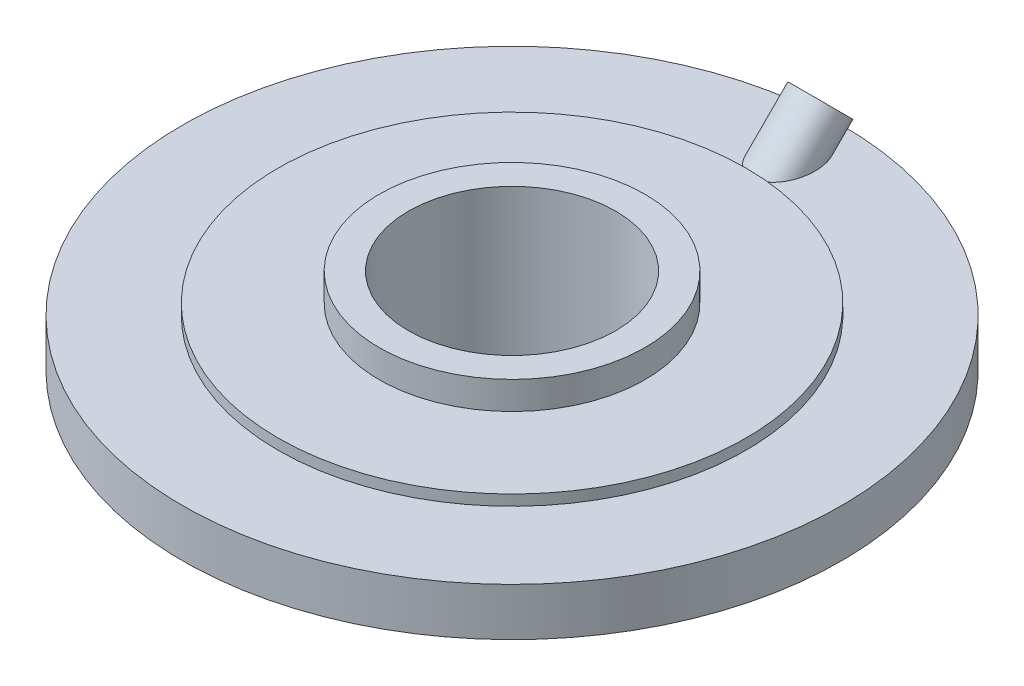
SolidWorks part; units mm, degrees
ref_plane "Front Plane" through (0, 0, 0) normal (0, 0, 1) x (1, 0, 0)
ref_plane "Top Plane" through (0, 0, 0) normal (0, 1, 0) x (1, 0, 0)
ref_plane "Right Plane" through (0, 0, 0) normal (1, 0, 0) x (0, 0, -1)
sketch "Sketch1" plane through (0, 0, 0) normal (0, 0, 1) x (1, 0, 0)
  line L0 (0, 0) -> (25, 0)
  line L1 (25, 0) -> (25, -5.2365)
  line L2 (25, -5.2365) -> (44, -5.2365)
  line L3 (44, -5.2365) -> (44, -7.2365)
  line L4 (44, -7.2365) -> (62, -7.2365)
  line L5 (62, -7.2365) -> (62, -16.2365)
  line L6 (62, -16.2365) -> (30.5, -16.2365)
  line L7 (30.5, -16.2365) -> (30.5, -19.2365)
  line L8 (30.5, -19.2365) -> (26, -19.2365)
  line L9 (26, -19.2365) -> (26, -38.0068)
  line L10 (26, -38.0068) -> (0, -38.0068)
  line L11 (0, -38.0068) -> (0, 0)
  point P3 (0, 0)
  point P14 (0, 0)
  point P15 (0, 0)
  point P16 (0, 0)
  point P17 (0, 0)
  dimension "D1" = 25
  dimension "D2" = 9
  dimension "D3" = 2
  dimension "D4" = 44
  dimension "D5" = 3
  dimension "D6" = 62
  dimension "D7" = 30.5
  dimension "D8" = 26
revolve "Revolve2" add sketch "Sketch1" angle 360 about L11
sketch "Sketch2" plane through (0, 0, 0) normal (0, 1, 0) x (1, 0, 0)
  circle A0 centre (0, 0) radius 19.5
  dimension "D1" = 39
extrude "Cut-Extrude1" cut sketch "Sketch2" against normal blind 90
sketch "Sketch4" plane through (0, 0, 0) normal (1, 0, 0) x (0, 0, -1)
  line L0 (52, -7.2365) -> (58, -1.2365)
  line L1 (62, -7.2365) -> (-62, -7.2365) construction
  line L2 (-62, -16.2365) -> (62, -16.2365) construction
  dimension "D1" = 45
  dimension "D2" = 15
  dimension "D3" = 58
ref_plane "Plane1" through (0, -1.2365, -58) normal (0, 0.7071, -0.7071) x (-1, 0, 0)
sketch "Sketch5" plane through (0, -1.2365, -58) normal (0, 0.7071, -0.7071) x (-1, 0, 0)
  circle A0 centre (0, 0) radius 5
  dimension "D1" = 10
extrude "Boss-Extrude1" add sketch "Sketch5" against normal up to surface (13.4853 mm away)
sketch "Sketch6" plane through (0, 28.3818, -28.3818) normal (0, 0.7071, -0.7071) x (1, 0, 0)
  circle A0 centre (0, 41.8865) radius 1.5
  dimension "D1" = 3
extrude "Cut-Extrude3" cut sketch "Sketch6" against normal blind 28
